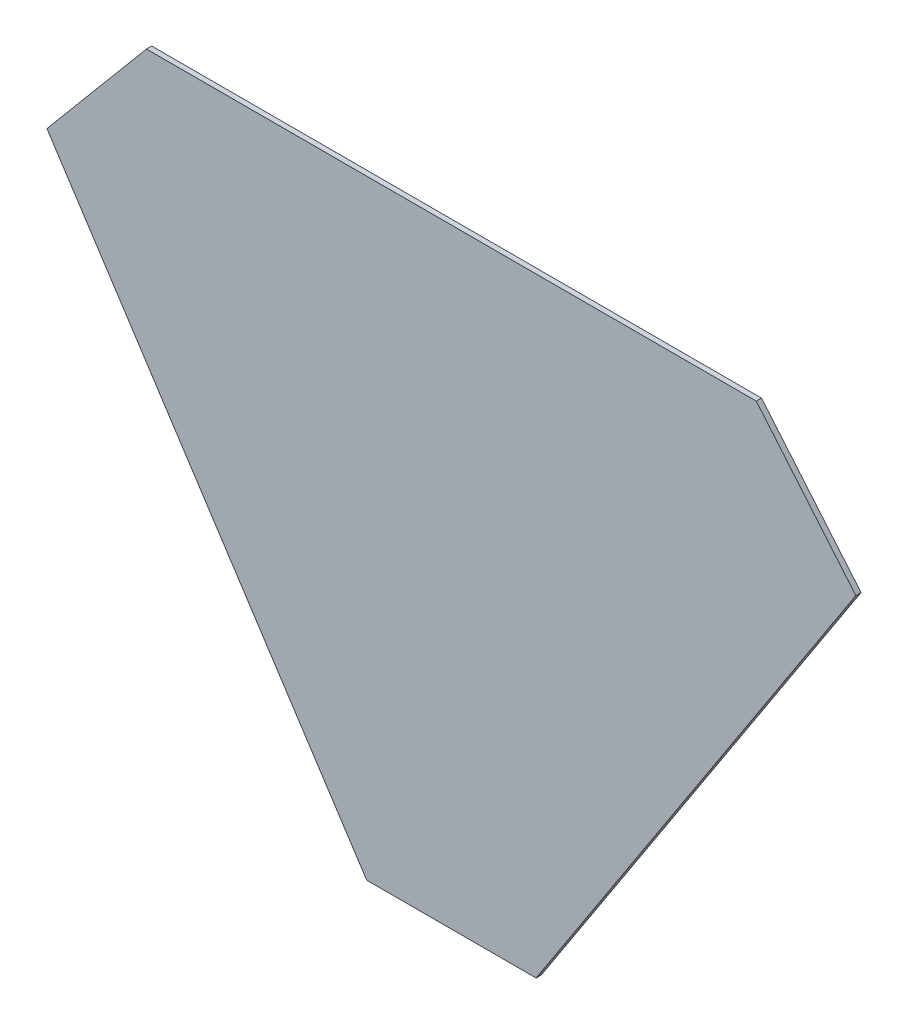
SolidWorks part; units mm, degrees
ref_plane "Plan de face" through (0, 0, 0) normal (0, 0, 1) x (1, 0, 0)
ref_plane "Plan de dessus" through (0, 0, 0) normal (0, 1, 0) x (1, 0, 0)
ref_plane "Plan de droite" through (0, 0, 0) normal (1, 0, 0) x (0, 0, -1)
sketch "Esquisse1" plane through (0, 0, 0) normal (0, 0, 1) x (1, 0, 0)
  line L0 (183.4207, 103.1332) -> (202.5362, 80.3522)
  line L1 (66.3479, 103.1332) -> (183.4207, 103.1332)
  line L5 (202.5362, 80.3522) -> (141.1439, -13.9242)
  line L6 (141.1439, -13.9242) -> (108.6247, -13.9242)
  line L7 (108.6247, -13.9242) -> (47.2324, 80.3522)
  line L8 (47.2324, 80.3522) -> (66.3479, 103.1332)
  line L11 (183.6538, 103.6332) -> (66.1147, 103.6332) construction
  line L12 (66.1147, 103.6332) -> (46.6112, 80.3898) construction
  line L13 (46.6112, 80.3898) -> (108.3536, -14.4242) construction
  line L14 (108.3536, -14.4242) -> (141.415, -14.4242) construction
  line L15 (141.415, -14.4242) -> (203.1573, 80.3898) construction
  line L16 (203.1573, 80.3898) -> (183.6538, 103.6332) construction
  point P8 (60.579, 22.6784)
  point P10 (-55.389, 43.3332)
  point P17 (37.45, -15.8235)
  dimension "D1" = 0.5
  dimension "D2" = 0.5
  dimension "D3" = 0.5
  dimension "D4" = 0.5
  dimension "D5" = 0.5
  dimension "D6" = 0.5
extrude "Boss.-Extru.1" add sketch "Esquisse1" along normal blind 1 contours L1 L0 L5 L6 L7 L8
